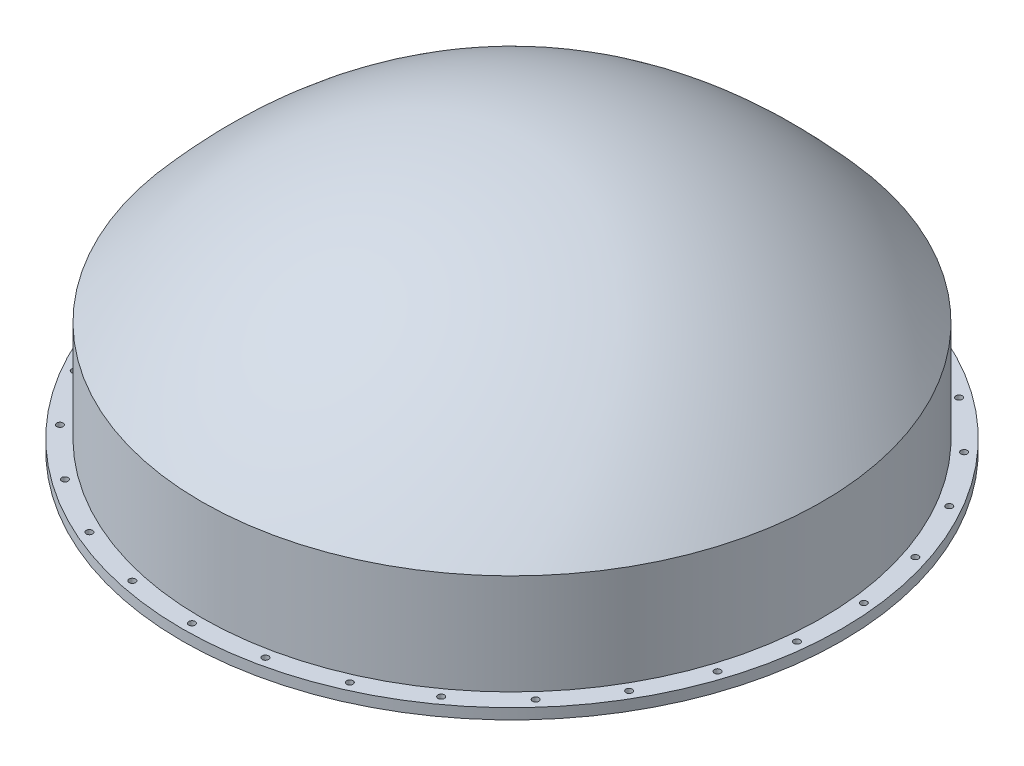
SolidWorks part; units mm, degrees
ref_plane "Front Plane" through (0, 0, 0) normal (0, 0, 1) x (1, 0, 0)
ref_plane "Top Plane" through (0, 0, 0) normal (0, 1, 0) x (1, 0, 0)
ref_plane "Right Plane" through (0, 0, 0) normal (1, 0, 0) x (0, 0, -1)
sketch "Sketch1" plane through (0, 0, 0) normal (1, 0, 0) x (0, 0, -1)
  line L0 (0, 2147.4608) -> (0, 0) construction
  line L1 (0, 0) -> (2586.9026, 0) construction
  line L2 (-2081.13, 0) -> (-2081.13, -744.115)
  line L3 (-931.3985, 1044.41) -> (931.3985, 1044.41) construction
  line L4 (-2130.02, 18.4154) -> (-2130.02, -671.115)
  line L5 (-2130.02, -671.115) -> (-2262.02, -671.115)
  line L6 (-2262.02, -671.115) -> (-2262.02, -744.115)
  line L7 (-2262.02, -744.115) -> (-2081.13, -744.115)
  line L8 (0, 1093.3) -> (0, 1044.41)
  line L9 (-2130.02, 18.4154) -> (-2130.02, -744.115) construction
  spline S0 degree 2 poles (0, 1044.41) (-1164.2481, 1044.41) (-2081.13, 0) knots 0 0 0 1 1 1
  spline S1 degree 1 poles (0, 1093.3) (-2130.02, 18.4154) knots 0 0 1 1 construction
  spline S2 degree 2 poles (0, 1093.3) (-111.9457, 1093.302) (-331.5497, 1074.3322) (-582.6566, 1030.0414) (-861.6415, 945.6732) (-1132.4042, 827.6537) (-1394.7843, 676.1416) (-1616.9632, 514.4202) (-1771.693, 383.3606) (-1878.1563, 284.3819) (-1953.2147, 209.8121) (-2005.296, 155.8083) (-2042.2513, 116.268) (-2068.0055, 88.139) (-2086.3399, 67.8055) (-2099.1459, 53.4589) (-2108.2763, 43.1526) (-2114.6664, 35.9036) (-2119.2082, 30.7311) (-2125.5097, 23.5529) (-2130.02, 18.4154) knots 0 0 0 0.094371 0.188742 0.31457 0.440399 0.566227 0.692055 0.786426 0.84934 0.896526 0.927983 0.951576 0.967304 0.9791 0.986965 0.992863 0.996795 0.999744 1.00171 1.006625 1.006625 1.006625
  point P8 (-2081.13, -372.0575)
  dimension "D1" = 2081.13
  dimension "D2" = 1044.41
  dimension "D3" = 744.115
  dimension "D5" = 132
  dimension "D6" = 73
  dimension "D4" = 48.89
revolve "Revolve1" add sketch "Sketch1" angle 360 about L8
sketch "Sketch2" plane through (0, -671.115, 0) normal (0, 1, 0) x (1, 0, 0)
  circle A0 centre (0, 0) radius 2196.0235 construction
  circle A1 centre (0, 2196.0235) radius 22
  circle A2 centre (456.579, 2148.0351) radius 22
  circle A3 centre (893.2032, 2006.1673) radius 22
  circle A4 centre (1290.7902, 1776.6203) radius 22
  circle A5 centre (1631.9635, 1469.4265) radius 22
  circle A6 centre (1901.8121, 1098.0118) radius 22
  circle A7 centre (2088.5425, 678.6086) radius 22
  circle A8 centre (2183.9935, 229.547) radius 22
  circle A9 centre (2183.9935, -229.547) radius 22
  circle A10 centre (2088.5425, -678.6086) radius 22
  circle A11 centre (1901.8121, -1098.0117) radius 22
  circle A12 centre (1631.9635, -1469.4265) radius 22
  circle A13 centre (1290.7902, -1776.6203) radius 22
  circle A14 centre (893.2032, -2006.1673) radius 22
  circle A15 centre (456.579, -2148.0351) radius 22
  circle A16 centre (0, -2196.0235) radius 22
  circle A17 centre (-456.579, -2148.0351) radius 22
  circle A18 centre (-893.2032, -2006.1673) radius 22
  circle A19 centre (-1290.7902, -1776.6203) radius 22
  circle A20 centre (-1631.9635, -1469.4265) radius 22
  circle A21 centre (-1901.8121, -1098.0118) radius 22
  circle A22 centre (-2088.5425, -678.6086) radius 22
  circle A23 centre (-2183.9935, -229.547) radius 22
  circle A24 centre (-2183.9935, 229.547) radius 22
  circle A25 centre (-2088.5425, 678.6086) radius 22
  circle A26 centre (-1901.8121, 1098.0117) radius 22
  circle A27 centre (-1631.9635, 1469.4265) radius 22
  circle A28 centre (-1290.7902, 1776.6203) radius 22
  circle A29 centre (-893.2032, 2006.1673) radius 22
  circle A30 centre (-456.579, 2148.0351) radius 22
  point P66 (0, 0)
  dimension "D1" = 30
extrude "Cut-Extrude1" cut sketch "Sketch2" against normal up to next (73 mm away)
